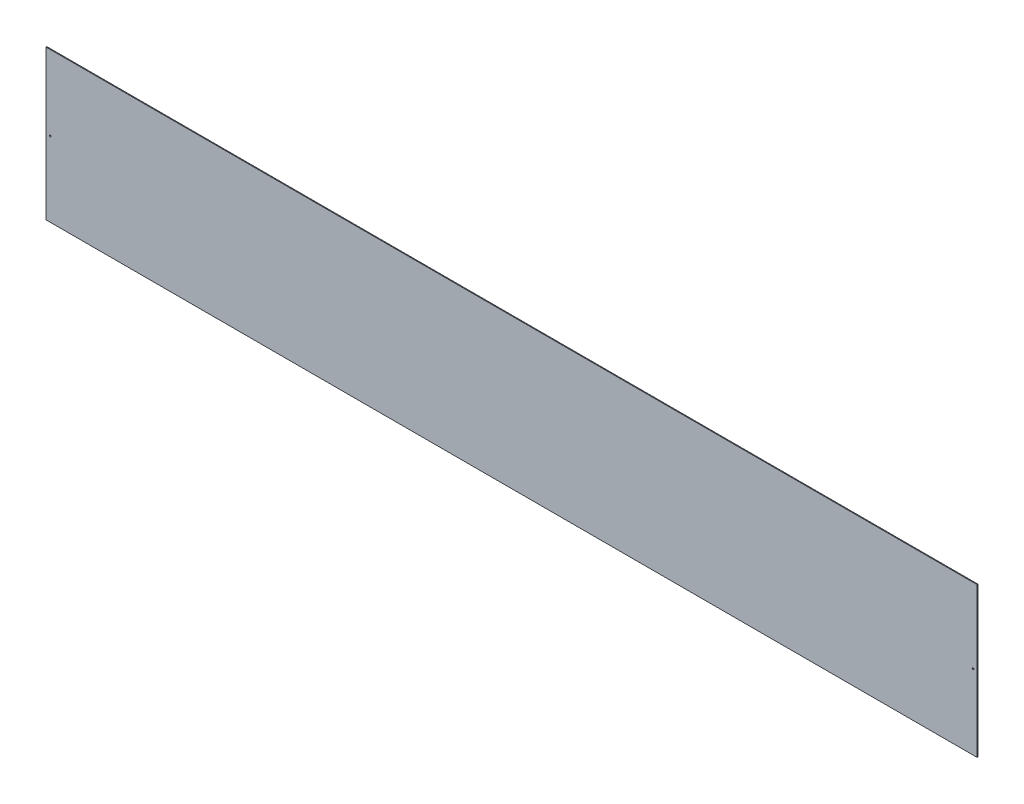
SolidWorks part; units mm, degrees
material "Glass"
ref_plane "Front Plane" through (0, 0, 0) normal (0, 0, 1) x (1, 0, 0)
ref_plane "Top Plane" through (0, 0, 0) normal (0, 1, 0) x (1, 0, 0)
ref_plane "Right Plane" through (0, 0, 0) normal (1, 0, 0) x (0, 0, -1)
sketch "Sketch1" plane through (0, 0, 0) normal (0, 0, 1) x (1, 0, 0)
  line L1 (-560, -90) -> (560, -90)
  line L2 (-560, -90) -> (-560, 90)
  line L3 (-560, 90) -> (560, 90)
  line L4 (560, -90) -> (560, 90)
  line L5 (-560, -90) -> (560, 90) construction
  line L6 (-560, 90) -> (560, -90) construction
  point P0 (0, 0)
extrude "Boss-Extrude1" add sketch "Sketch1" along normal blind 1
sketch "Sketch2" plane through (0, 0, 0) normal (0, 0, -1) x (-1, 0, 0)
  line L1 (-560, -90) -> (-560, 90) construction
  circle A0 centre (-555, 0) radius 1
  point P2 (-555, 0)
  dimension "D1" = 5
extrude "Cut-Extrude1" cut sketch "Sketch2" against normal through all
mirror "Mirror1" about plane through (0, 0, 0) normal (1, 0, 0) of "Cut-Extrude1"
